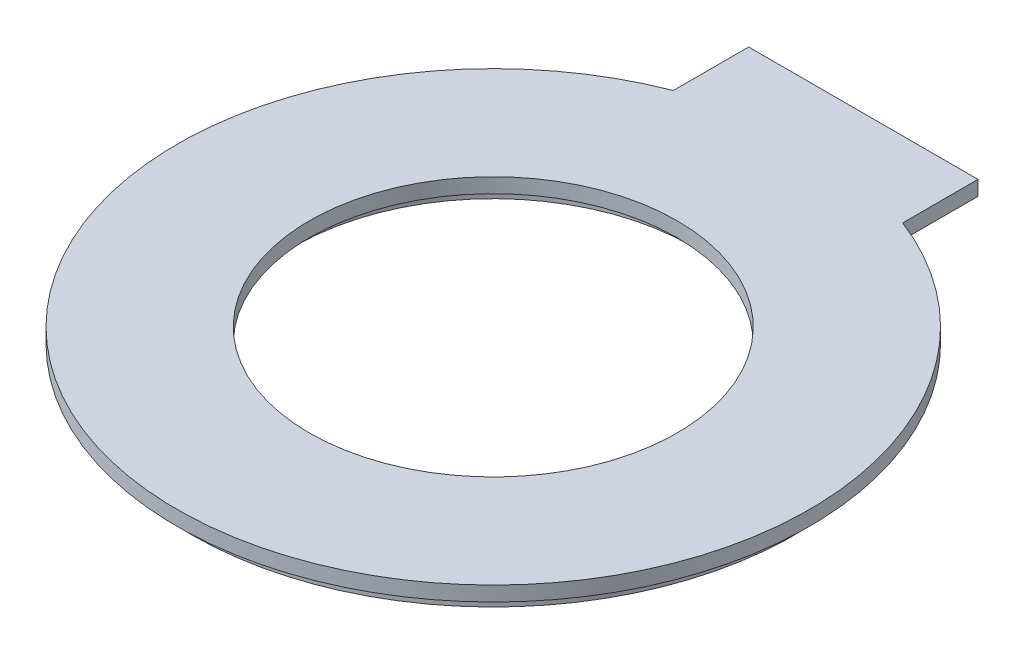
SolidWorks part; units mm, degrees
ref_plane "Front Plane" through (0, 0, 0) normal (0, 0, 1) x (1, 0, 0)
ref_plane "Top Plane" through (0, 0, 0) normal (0, 1, 0) x (1, 0, 0)
ref_plane "Right Plane" through (0, 0, 0) normal (1, 0, 0) x (0, 0, -1)
sketch "Sketch1" plane through (0, 0, 0) normal (0, 1, 0) x (1, 0, 0)
  line L0 (0, 0) -> (0, 77.1311) construction
  line L3 (-7.795, 20.0372) -> (-7.795, 25.1572)
  line L4 (-7.795, 25.1572) -> (7.795, 25.1572)
  line L5 (7.795, 20.0372) -> (7.795, 25.1572)
  circle A0 centre (0, 0) radius 12.5
  arc A1 (-7.795, 20.0372) -> (7.795, 20.0372) centre (0, 0) ccw
  point P9 (-7.795, 20.0372)
  point P11 (0, 0)
  dimension "D1" = 15.59
  dimension "D3" = 21.5
  dimension "D4" = 25
  dimension "D2" = 5.12
extrude "Boss-Extrude1" add sketch "Sketch1" along normal blind 1
sketch "Sketch2" plane through (0, 0, 0) normal (0, -1, 0) x (1, 0, 0)
  line L0 (-7.795, -25.1572) -> (-7.795, -20.0372) construction
  line L1 (-6.795, -24.1572) -> (6.795, -24.1572)
  line L2 (-6.795, -24.1572) -> (-6.795, -19.3411)
  line L4 (6.795, -24.1572) -> (6.795, -19.3411)
  line L5 (7.795, -20.0372) -> (7.795, -25.1572) construction
  line L6 (7.795, -25.1572) -> (-7.795, -25.1572) construction
  arc A0 (6.795, -19.3411) -> (-6.795, -19.3411) centre (0, 0) ccw
  circle A1 centre (0, 0) radius 13.5
  circle A2 centre (0, 0) radius 12.5 construction
  circle A3 centre (0, 0) radius 21.5 construction
  dimension "D1" = 1
  dimension "D2" = 1
  dimension "D3" = 1
  dimension "D4" = 1
  dimension "D5" = 1
extrude "Boss-Extrude2" add sketch "Sketch2" along normal blind 1
